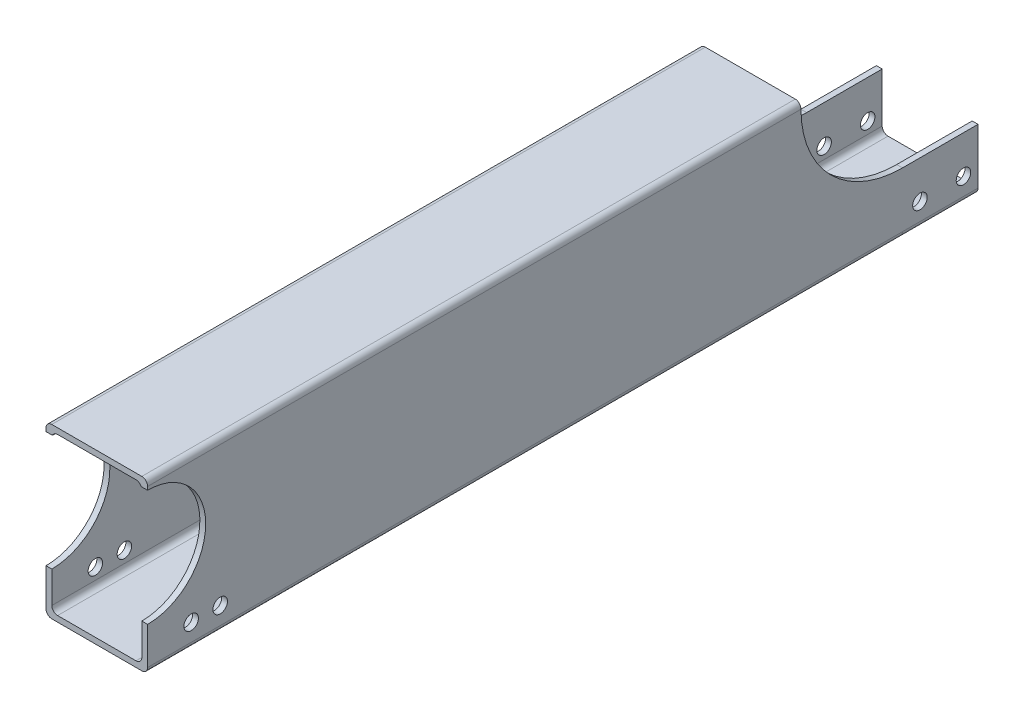
SolidWorks part; units mm, degrees
ref_plane "Front Plane" through (0, 0, 0) normal (0, 0, 1) x (1, 0, 0)
ref_plane "Top Plane" through (0, 0, 0) normal (0, 1, 0) x (1, 0, 0)
ref_plane "Right Plane" through (0, 0, 0) normal (1, 0, 0) x (0, 0, -1)
sketch "Sketch1" plane through (0, 0, 0) normal (0, 0, 1) x (1, 0, 0)
  line L1 (-9.8668, 32.238) -> (25.1332, 32.238)
  line L2 (-9.8668, 32.238) -> (-9.8668, -25.762)
  line L3 (-9.8668, -25.762) -> (25.1332, -25.762)
  line L4 (25.1332, 32.238) -> (25.1332, -25.762)
  line L5 (-7.8668, 30.238) -> (23.1332, 30.238)
  line L6 (-7.8668, 30.238) -> (-7.8668, -23.762)
  line L7 (-7.8668, -23.762) -> (23.1332, -23.762)
  line L8 (23.1332, 30.238) -> (23.1332, -23.762)
  dimension "D1" = 35
  dimension "D2" = 58
  dimension "D3" = 2
  dimension "D4" = 2
  dimension "D5" = 2
  dimension "D6" = 2
extrude "Extrude1" add sketch "Sketch1" along normal blind 260
fillet "Fillet1" radius 2 8 edges at (23.1332, -23.762, 130) (-7.8668, 30.238, 130) (-9.8668, -25.762, 130) (23.1332, 30.238, 130) (-7.8668, -23.762, 130) (25.1332, -25.762, 130) (-9.8668, 32.238, 130) (25.1332, 32.238, 130)
sketch "Sketch2" plane through (-9.8668, 0, 0) normal (-1, 0, 0) x (0, 0, 1)
  line L0 (260, 30.238) -> (260, -23.762) construction
  line L1 (260, -25.762) -> (0, -25.762) construction
  circle A0 centre (245, -17.762) radius 2.5
  circle A1 centre (235, -17.762) radius 2.5
  dimension "D2" = 5
  dimension "D3" = 5
  dimension "D1" = 10
  dimension "D4" = 15
  dimension "D5" = 8
  dimension "D6" = 8
extrude "Extrude2" cut sketch "Sketch2" against normal blind 203.8
sketch "Sketch3" plane through (-9.8668, 0, 0) normal (-1, 0, 0) x (0, 0, 1)
  line L0 (260, -25.762) -> (0, -25.762) construction
  circle A0 centre (199, -17.762) radius 2.5
  circle A1 centre (235, -17.762) radius 2.5 construction
  dimension "D1" = 5
  dimension "D3" = 36
  dimension "D2" = 8
extrude "Extrude3" cut sketch "Sketch3" against normal blind 10
sketch "Sketch5" plane through (0, 0, 0) normal (0, 0, -1) x (-1, 0, 0)
  line L0 (-25.1332, -4.7396) -> (-25.1332, -23.762)
  line L1 (-25.1332, -23.762) -> (-25.1332, 30.238) construction
  line L2 (-25.1332, -23.762) -> (-25.1332, -25.762)
  line L3 (-25.1332, -25.762) -> (7.8668, -25.762)
  line L4 (7.8668, -25.762) -> (9.8668, -25.762)
  line L5 (9.8668, -25.762) -> (9.8668, -4.7396)
  line L6 (9.8668, 30.238) -> (9.8668, -23.762) construction
  line L7 (9.8668, -4.7396) -> (7.8668, -4.7396)
  line L8 (7.8668, 28.238) -> (7.8668, -21.762) construction
  line L9 (7.8668, -4.7396) -> (7.8668, -21.762)
  line L10 (7.8668, -21.762) -> (7.8668, -23.762)
  line L11 (7.8668, -23.762) -> (-23.1332, -23.762)
  line L12 (-23.1332, -23.762) -> (-23.1332, -4.7396)
  line L13 (-23.1332, -21.762) -> (-23.1332, 28.238) construction
  line L14 (-23.1332, -4.7396) -> (-25.1332, -4.7396)
extrude "Extrude5" add sketch "Sketch5" along normal blind 26
fillet "Fillet6" radius 2 1 edges at (25.1332, -25.762, -13)
fillet "Fillet7" radius 2 1 edges at (-9.8668, -25.762, -13)
fillet "Fillet8" radius 2 1 edges at (23.1332, -23.762, -13)
fillet "Fillet9" radius 2 1 edges at (-7.8668, -23.762, -13)
sketch "Sketch7" plane through (-9.8668, 0, 0) normal (-1, 0, 0) x (0, 0, 1)
  line L0 (0, -25.762) -> (-26, -25.762) construction
  line L1 (260, -25.762) -> (0, -25.762) construction
  line L2 (-26, -23.762) -> (-26, -4.7396) construction
  circle A0 centre (-6, -17.762) radius 2.5
  circle A1 centre (-21, -17.762) radius 2.5
  dimension "D5" = 5
  dimension "D6" = 5
  dimension "D1" = 8
  dimension "D2" = 8
  dimension "D3" = 15
  dimension "D4" = 5
extrude "Extrude6" cut sketch "Sketch7" against normal through all
sketch "Sketch8" plane through (-9.8668, 0, 0) normal (-1, 0, 0) x (0, 0, 1)
  line L0 (260, 30.238) -> (260, -23.762) construction
  circle A0 centre (260, 9.0974) radius 20
  circle A1 centre (0, 30.238) radius 34.9776
  dimension "D1" = 40
extrude "Extrude7" cut sketch "Sketch8" against normal through all
